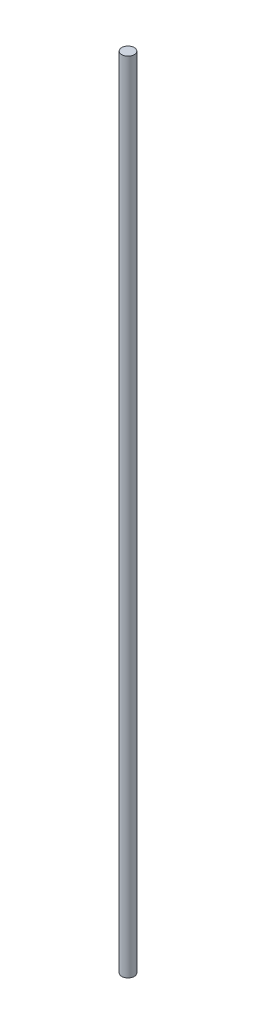
SolidWorks part; units mm, degrees
ref_plane "Front Plane" through (0, 0, 0) normal (0, 0, 1) x (1, 0, 0)
ref_plane "Top Plane" through (0, 0, 0) normal (0, 1, 0) x (1, 0, 0)
ref_plane "Right Plane" through (0, 0, 0) normal (1, 0, 0) x (0, 0, -1)
sketch "Sketch1" plane through (0, 0, 0) normal (0, 1, 0) x (1, 0, 0)
  circle A0 centre (0, 0) radius 2.3813
  dimension "D1" = 4.7625
extrude "Boss-Extrude1" add sketch "Sketch1" along normal blind 304.8
